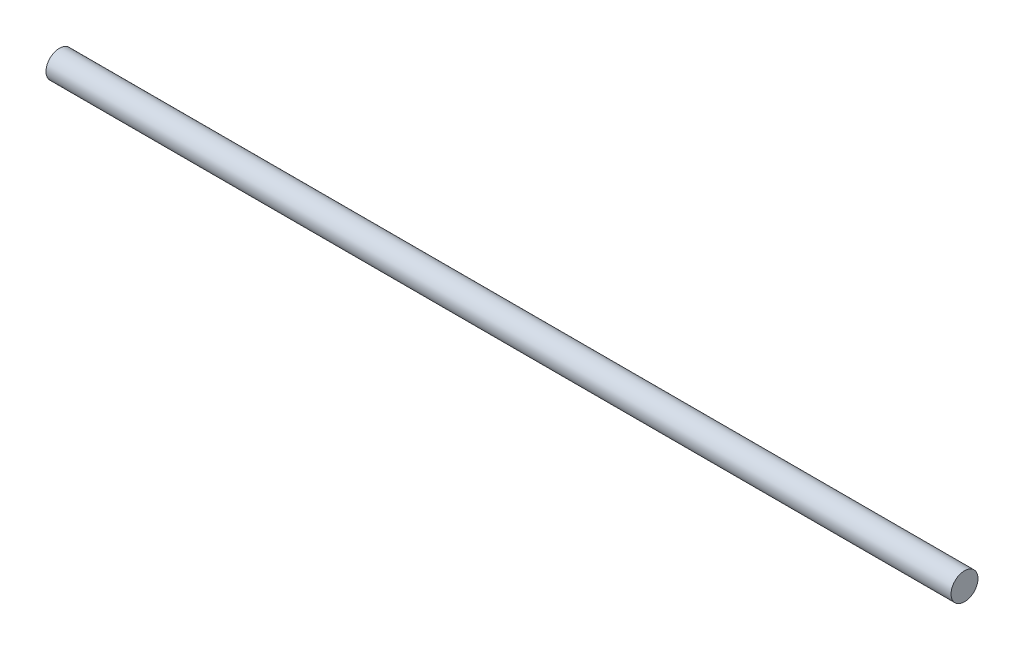
SolidWorks part; units mm, degrees
ref_plane "Front Plane" through (0, 0, 0) normal (0, 0, 1) x (1, 0, 0)
ref_plane "Top Plane" through (0, 0, 0) normal (0, 1, 0) x (1, 0, 0)
ref_plane "Right Plane" through (0, 0, 0) normal (1, 0, 0) x (0, 0, -1)
sketch "Sketch1" plane through (0, 0, 0) normal (1, 0, 0) x (0, 0, -1)
  circle A0 centre (0, 0) radius 4.765
  dimension "D1" = 9.53
extrude "Boss-Extrude1" add sketch "Sketch1" along normal blind 320
